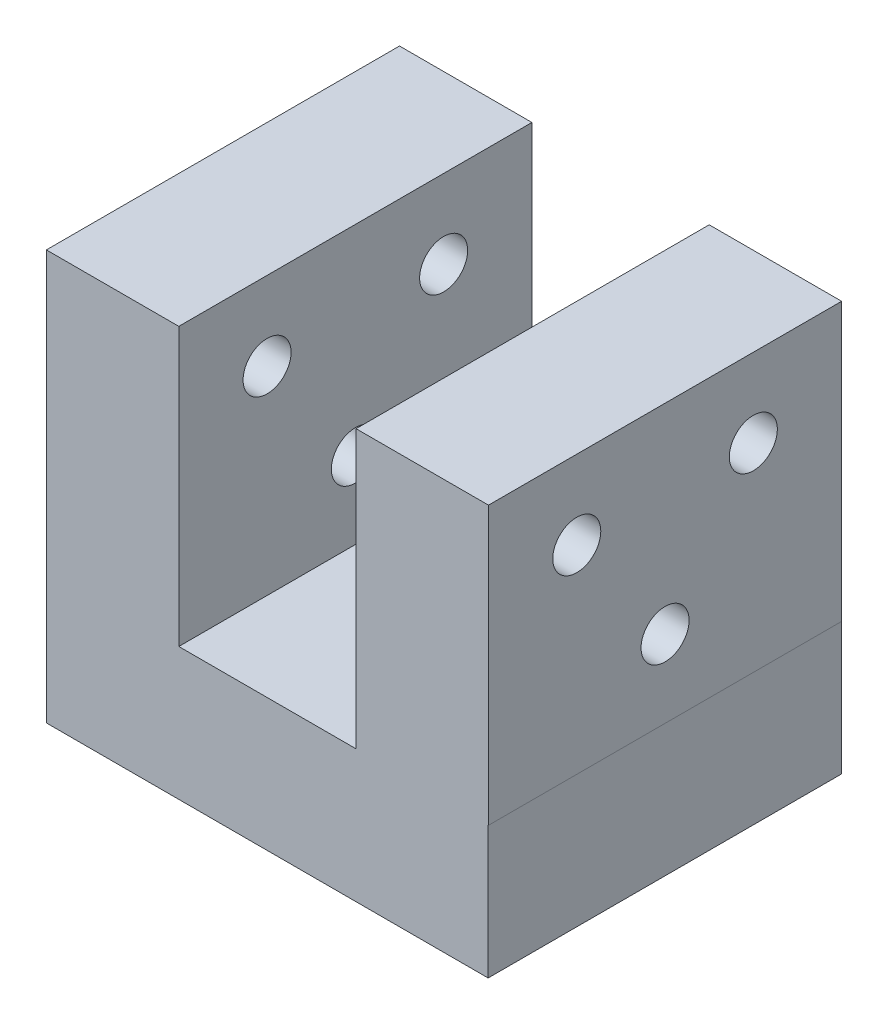
SolidWorks part; units mm, degrees
material "Onyx w/ CF"
ref_plane "Front Plane" through (0, 0, 0) normal (0, 0, 1) x (1, 0, 0)
ref_plane "Top Plane" through (0, 0, 0) normal (0, 1, 0) x (1, 0, 0)
ref_plane "Right Plane" through (0, 0, 0) normal (1, 0, 0) x (0, 0, -1)
sketch "Sketch1" plane through (0, 0, 0) normal (0, 1, 0) x (1, 0, 0)
  line L1 (-15.875, 12.7) -> (15.875, 12.7)
  line L2 (-15.875, 12.7) -> (-15.875, -12.7)
  line L3 (-15.875, -12.7) -> (15.875, -12.7)
  line L4 (15.875, 12.7) -> (15.875, -12.7)
  line L5 (-15.875, 12.7) -> (15.875, -12.7) construction
  line L6 (-15.875, -12.7) -> (15.875, 12.7) construction
  point P0 (0, 0)
  dimension "D1" = 31.75
  dimension "D2" = 25.4
extrude "Boss-Extrude1" add sketch "Sketch1" along normal blind 9.525
hole_wizard "M2.5 Clearance Hole1" positions "3DSketch1" profile "Sketch2" hole size "M2.5" standard "ANSI Metric"
sketch3d "3DSketch1"
  line L1 (8, 0, -8) -> (8, 0, 8)
  line L2 (8, 0, -8) -> (-8, 0, -8)
  line L3 (-8, 0, -8) -> (-8, 0, 8)
  line L4 (8, 0, 8) -> (-8, 0, 8)
  line L5 (8, 0, -8) -> (-8, 0, 8) construction
  line L6 (-8, 0, -8) -> (8, 0, 8) construction
  point P0 (8, 0, -8)
  point P2 (8, 0, 8)
  point P4 (-8, 0, 8)
  point P6 (-8, 0, -8)
  point P11 (0, 0, 0)
  dimension "D1" = 16
sketch "Sketch2" plane through (8, 0, -8) normal (1, 0, 0) x (0, 0, -1)
  line L0 (0, 0) -> (0, 8.9323)
  line L1 (0, 8.9323) -> (1.55, 8.001)
  line L2 (1.55, 8.001) -> (1.55, 0)
  line L5 (1.55, 0) -> (0, 0)
  line L10 (0, 8.9323) -> (-1.55, 8.001) construction
  line L11 (0, -6.35) -> (0, 107.95) construction
  dimension "Hole Dia." = 3.1
  dimension "Hole Depth" = 8.001
  dimension "Drill Angle" = 118
sketch "Sketch3" plane through (0, 0, -12.7) normal (0, 0, -1) x (-1, 0, 0)
  line L0 (-15.875, 9.525) -> (15.875, 9.525) construction
  line L1 (15.9004, 9.525) -> (6.3754, 9.525)
  line L2 (15.9004, 9.525) -> (15.9004, 29.4675)
  line L3 (15.9004, 29.4675) -> (6.3754, 29.4675)
  line L4 (6.3754, 9.525) -> (6.3754, 29.4675)
  line L5 (6.3754, 29.4675) -> (-6.3754, 29.4675) construction
  line L6 (-6.3754, 9.525) -> (-15.9004, 9.525)
  line L7 (-6.3754, 9.525) -> (-6.3754, 29.4675)
  line L8 (-6.3754, 29.4675) -> (-15.9004, 29.4675)
  line L9 (-15.9004, 9.525) -> (-15.9004, 29.4675)
  line L10 (-15.875, 0) -> (15.875, 0) construction
  point P10 (0, 29.4675)
  point P13 (0, 0)
  dimension "D1" = 9.525
  dimension "D2" = 12.7508
  dimension "D3" = 19.9425
extrude "Boss-Extrude2" add sketch "Sketch3" against normal up to surface (25.4 mm away) up to face at (0, 4.7625, 12.7)
hole_wizard "#4 Clearance Hole1" positions "Sketch6" profile "Sketch8" hole size "#4" standard "ANSI Inch" end condition through all
sketch "Sketch6" plane through (15.9004, 0, 0) normal (1, 0, 0) x (0, 0, -1)
  line L1 (3.175, 18.2562) -> (-3.175, 18.2562)
  line L2 (3.175, 18.2562) -> (3.175, 11.9062)
  line L3 (3.175, 11.9062) -> (-3.175, 11.9062)
  line L4 (-3.175, 18.2562) -> (-3.175, 11.9062)
  line L5 (-12.7, 9.525) -> (12.7, 9.525) construction
  line L7 (9.525, 26.9875) -> (3.175, 26.9875)
  line L8 (9.525, 26.9875) -> (9.525, 20.6375)
  line L9 (9.525, 20.6375) -> (3.175, 20.6375)
  line L10 (3.175, 26.9875) -> (3.175, 20.6375)
  line L12 (-3.175, 26.9875) -> (-9.525, 26.9875)
  line L13 (-3.175, 26.9875) -> (-3.175, 20.6375)
  line L14 (-3.175, 20.6375) -> (-9.525, 20.6375)
  line L15 (-9.525, 26.9875) -> (-9.525, 20.6375)
  line L16 (-12.7, 9.525) -> (-12.7, 29.4675) construction
  line L17 (12.7, 29.4675) -> (12.7, 9.525) construction
  point P0 (0, 15.0812)
  point P2 (6.35, 23.8125)
  point P4 (-6.35, 23.8125)
  point P98 (0, 18.2562)
  point P99 (3.175, 15.0812)
  point P179 (6.35, 20.6375)
  point P180 (9.525, 23.8125)
  point P181 (-6.35, 20.6375)
  point P183 (-3.175, 23.8125)
  dimension "D1" = 6.35
  dimension "D2" = 2.3812
  dimension "D3" = 3.175
  dimension "D4" = 3.175
  dimension "D5" = 2.3812
sketch "Sketch8" plane through (15.9004, 15.0812, 0) normal (0, 1, 0) x (0, 0, -1)
  line L0 (0, 0) -> (0, 31.8008)
  line L1 (0, 31.8008) -> (1.7272, 31.8008)
  line L2 (1.7272, 31.8008) -> (1.7272, 0)
  line L5 (1.7272, 0) -> (0, 0)
  line L11 (0, -6.35) -> (0, 107.95) construction
  dimension "Thru Hole Dia." = 3.4544
  dimension "Thru Hole Depth" = 31.8008
ref_plane "Plane1" through (11.1379, 0, 0) normal (1, 0, 0) x (0, 0, -1)
sketch "Sketch9" plane through (11.1379, 0, 0) normal (1, 0, 0) x (0, 0, -1)
  line L1 (9.2988, 26.7613) -> (3.4012, 26.7613)
  line L2 (9.2988, 26.7613) -> (9.2988, 20.8637)
  line L3 (9.2988, 20.8637) -> (3.4012, 20.8637)
  line L4 (3.4012, 26.7613) -> (3.4012, 20.8637)
  line L5 (9.2988, 26.7613) -> (3.4012, 20.8637) construction
  line L6 (9.2988, 20.8637) -> (3.4012, 26.7613) construction
  line L7 (2.9488, 18.03) -> (-2.9488, 18.03)
  line L8 (2.9488, 18.03) -> (2.9488, 12.1325)
  line L9 (2.9488, 12.1325) -> (-2.9488, 12.1325)
  line L10 (-2.9488, 18.03) -> (-2.9488, 12.1325)
  line L11 (2.9488, 18.03) -> (-2.9488, 12.1325) construction
  line L12 (2.9488, 12.1325) -> (-2.9488, 18.03) construction
  line L13 (-3.4012, 26.7613) -> (-9.2988, 26.7613)
  line L14 (-3.4012, 26.7613) -> (-3.4012, 20.8637)
  line L15 (-3.4012, 20.8637) -> (-9.2988, 20.8637)
  line L16 (-9.2988, 26.7613) -> (-9.2988, 20.8637)
  line L17 (-3.4012, 26.7613) -> (-9.2988, 20.8637) construction
  line L18 (-3.4012, 20.8637) -> (-9.2988, 26.7613) construction
  point P0 (6.35, 23.8125)
  point P6 (0, 15.0812)
  point P12 (-6.35, 23.8125)
  dimension "D1" = 5.8975
extrude "Cut-Extrude1" cut sketch "Sketch9" against normal mid plane 2.1891
ref_plane "Plane2" through (0, 4.7625, 0) normal (0, -1, 0) x (-1, 0, 0)
sketch "Sketch10" plane through (0, 4.7625, 0) normal (0, -1, 0) x (-1, 0, 0)
  line L1 (-10.7265, 11.025) -> (-5.2735, 11.025)
  line L2 (-10.7265, 11.025) -> (-10.7265, 4.9751)
  line L3 (-10.7265, 4.9751) -> (-5.2735, 4.9751)
  line L4 (-5.2735, 11.025) -> (-5.2735, 4.9751)
  line L5 (-10.7265, 11.025) -> (-5.2735, 4.9751) construction
  line L6 (-10.7265, 4.9751) -> (-5.2735, 11.025) construction
  line L7 (5.2735, 11.0249) -> (10.7265, 11.0249)
  line L8 (5.2735, 11.0249) -> (5.2735, 4.975)
  line L9 (5.2735, 4.975) -> (10.7265, 4.975)
  line L10 (10.7265, 11.0249) -> (10.7265, 4.975)
  line L11 (5.2735, 11.0249) -> (10.7265, 4.975) construction
  line L12 (5.2735, 4.975) -> (10.7265, 11.0249) construction
  line L13 (5.2735, -4.9751) -> (10.7265, -4.9751)
  line L14 (5.2735, -4.9751) -> (5.2735, -11.025)
  line L15 (5.2735, -11.025) -> (10.7265, -11.025)
  line L16 (10.7265, -4.9751) -> (10.7265, -11.025)
  line L17 (5.2735, -4.9751) -> (10.7265, -11.025) construction
  line L18 (5.2735, -11.025) -> (10.7265, -4.9751) construction
  line L19 (-10.7265, -4.9751) -> (-5.2735, -4.9751)
  line L20 (-10.7265, -4.9751) -> (-10.7265, -11.025)
  line L21 (-10.7265, -11.025) -> (-5.2735, -11.025)
  line L22 (-5.2735, -4.9751) -> (-5.2735, -11.025)
  line L23 (-10.7265, -4.9751) -> (-5.2735, -11.025) construction
  line L24 (-10.7265, -11.025) -> (-5.2735, -4.9751) construction
  point P0 (-8, 8)
  point P6 (8, 8)
  point P12 (8, -8)
  point P18 (-8, -8)
  dimension "D1" = 5.453
  dimension "D2" = 6.0499
extrude "Cut-Extrude2" cut sketch "Sketch10" against normal mid plane 2.3542
